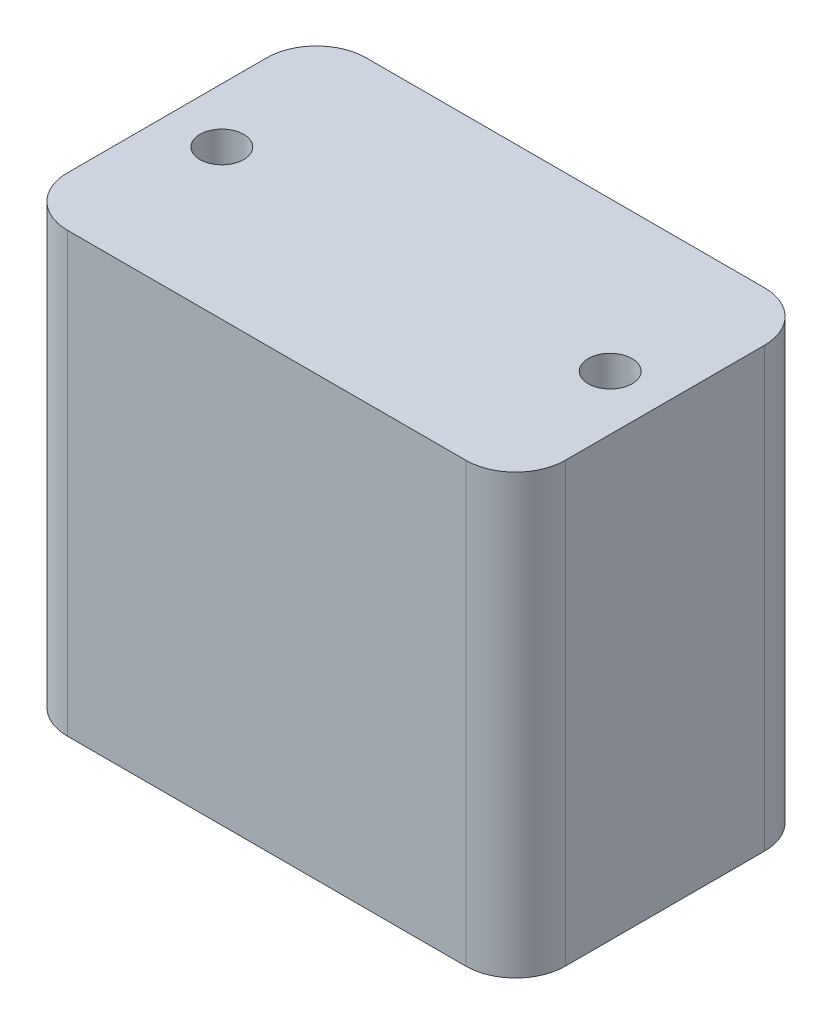
SolidWorks part; units mm, degrees
ref_plane "Front Plane" through (0, 0, 0) normal (0, 0, 1) x (1, 0, 0)
ref_plane "Top Plane" through (0, 0, 0) normal (0, 1, 0) x (1, 0, 0)
ref_plane "Right Plane" through (0, 0, 0) normal (1, 0, 0) x (0, 0, -1)
sketch "Sketch1" plane through (0, 0, 0) normal (0, 1, 0) x (1, 0, 0)
  line L0 (0, -55) -> (0, 55) construction
  line L1 (20, -15) -> (-20, -15)
  line L2 (25, -10) -> (25, 10)
  line L3 (20, 15) -> (-20, 15)
  line L4 (-25, -10) -> (-25, 10)
  line L5 (25, -15) -> (-25, 15) construction
  line L6 (25, 15) -> (-25, -15) construction
  circle A0 centre (-19.5, 0) radius 2.2
  circle A1 centre (19.5, 0) radius 2.2
  arc A2 (20, -15) -> (25, -10) centre (20, -10) ccw
  arc A3 (25, 10) -> (20, 15) centre (20, 10) ccw
  arc A4 (-20, -15) -> (-25, -10) centre (-20, -10) cw
  arc A5 (-20, 15) -> (-25, 10) centre (-20, 10) ccw
  point P0 (0, 0)
  dimension "D3" = 19.5
  dimension "D4" = 5
  dimension "D1" = 50
  dimension "D2" = 30
extrude "Boss-Extrude1" add sketch "Sketch1" along normal blind 44
